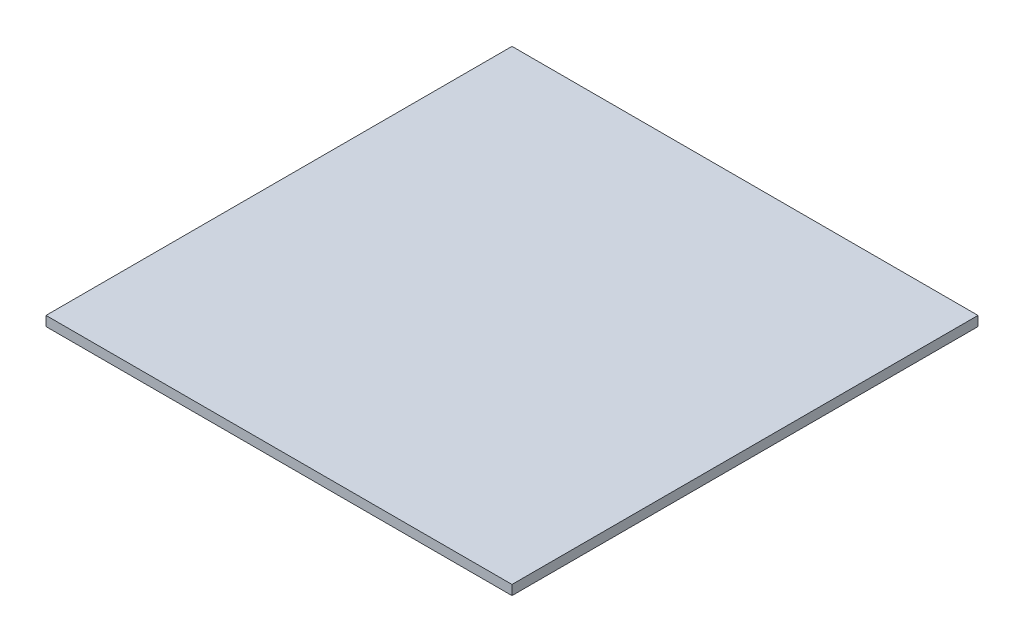
SolidWorks part; units mm, degrees
ref_plane "Front Plane" through (0, 0, 0) normal (0, 0, 1) x (1, 0, 0)
ref_plane "Top Plane" through (0, 0, 0) normal (0, 1, 0) x (1, 0, 0)
ref_plane "Right Plane" through (0, 0, 0) normal (1, 0, 0) x (0, 0, -1)
sketch "Sketch1" plane through (0, 0, 0) normal (0, 1, 0) x (1, 0, 0)
  line L1 (-152.4, -152.4) -> (152.4, -152.4)
  line L2 (-152.4, -152.4) -> (-152.4, 152.4)
  line L3 (-152.4, 152.4) -> (152.4, 152.4)
  line L4 (152.4, -152.4) -> (152.4, 152.4)
  point P4 (247.8593, 152.4)
  point P5 (0, 152.4)
  point P7 (152.4, 0)
  dimension "D1" = 304.8
extrude "Boss-Extrude1" add sketch "Sketch1" along normal blind 6.35
